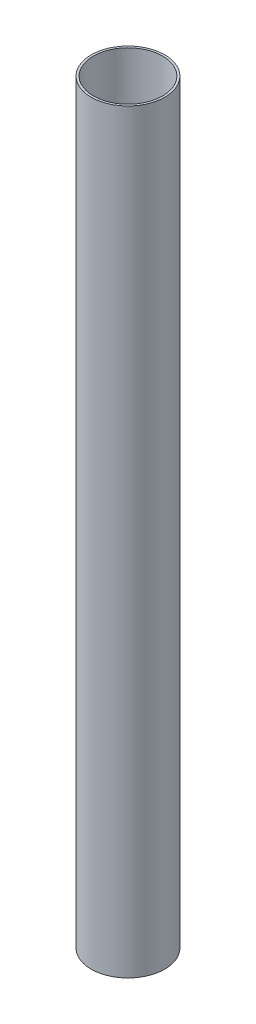
SolidWorks part; units mm, degrees
material "Phenolic Fiber Filled"
ref_plane "Front Plane" through (0, 0, 0) normal (0, 0, 1) x (1, 0, 0)
ref_plane "Top Plane" through (0, 0, 0) normal (0, 1, 0) x (1, 0, 0)
ref_plane "Right Plane" through (0, 0, 0) normal (1, 0, 0) x (0, 0, -1)
sketch "Sketch1" plane through (0, 0, 0) normal (0, 1, 0) x (1, 0, 0)
  circle A0 centre (0, 0) radius 45.5803
  circle A1 centre (0, 0) radius 42.926
  dimension "D1" = 91.1606
  dimension "D2" = 85.852
extrude "Extrude1" add sketch "Sketch1" along normal blind 936.625
